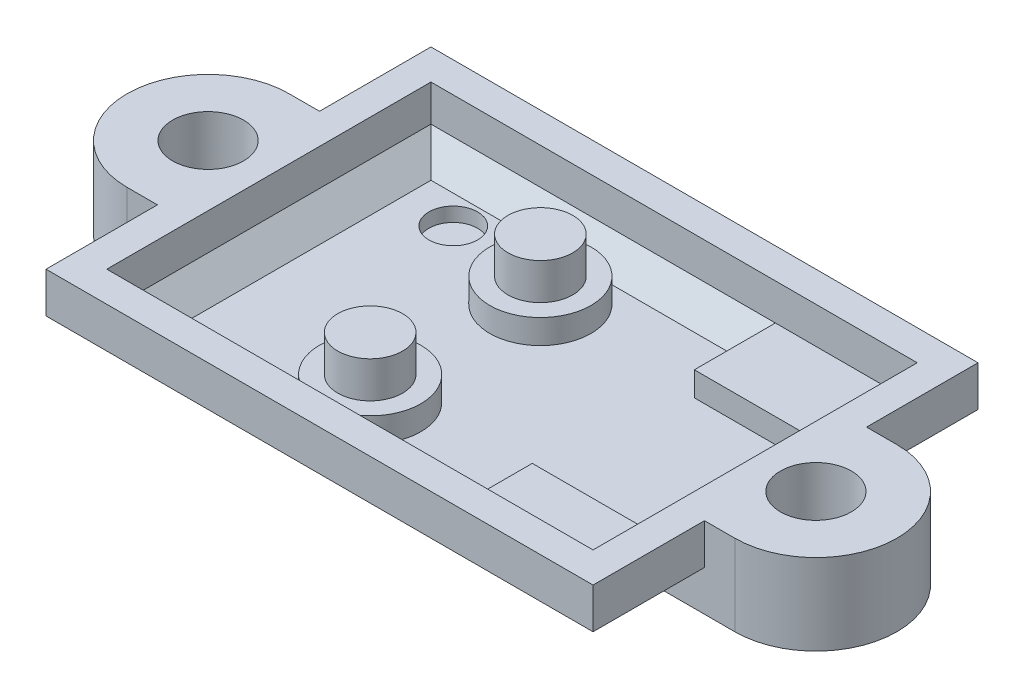
SolidWorks part; units mm, degrees
material "ABS"
ref_plane "Спереди" through (0, 0, 0) normal (0, 0, 1) x (1, 0, 0)
ref_plane "Сверху" through (0, 0, 0) normal (0, 1, 0) x (1, 0, 0)
ref_plane "Справа" through (0, 0, 0) normal (1, 0, 0) x (0, 0, -1)
sketch "Размеры платы" plane through (0, 0, 0) normal (0, 1, 0) x (1, 0, 0)
  line L1 (-10.9, -6.95) -> (10.9, -6.95) construction
  line L2 (-10.9, -6.95) -> (-10.9, 6.95) construction
  line L3 (-10.9, 6.95) -> (10.9, 6.95) construction
  line L4 (10.9, -6.95) -> (10.9, 6.95) construction
  line L5 (-10.9, -6.95) -> (10.9, 6.95) construction
  line L6 (-10.9, 6.95) -> (10.9, -6.95) construction
  point P0 (0, 0)
sketch "Внешние стенки" plane through (0, 0, 0) normal (0, 1, 0) x (1, 0, 0)
  line L0 (-15, 4) -> (-13.5, 4)
  line L1 (13.5, -9.5) -> (-13.5, -9.5)
  line L2 (13.5, -9.5) -> (13.5, 9.5) construction
  line L3 (13.5, 9.5) -> (-13.5, 9.5)
  line L4 (-13.5, -9.5) -> (-13.5, 9.5) construction
  line L5 (13.5, -9.5) -> (-13.5, 9.5) construction
  line L6 (13.5, 9.5) -> (-13.5, -9.5) construction
  line L7 (-15, -4) -> (-13.5, -4)
  line L8 (-13.5, 4) -> (-13.5, 9.5)
  line L9 (-13.5, -4) -> (-13.5, -9.5)
  line L10 (15, 4) -> (13.5, 4)
  line L11 (13.5, 4) -> (13.5, 9.5)
  line L12 (15, -4) -> (13.5, -4)
  line L13 (13.5, -4) -> (13.5, -9.5)
  arc A0 (-15, 4) -> (-15, -4) centre (-15, 0) ccw
  arc A1 (15, 4) -> (15, -4) centre (15, 0) cw
  circle A2 centre (-15, 0) radius 1.75
  circle A3 centre (15, 0) radius 1.75
  point P1 (0, 0)
extrude "Бобышка-Вытянуть1" add sketch "Внешние стенки" along normal blind 4
chamfer "Фаска1" distance 1.5 angle 45 2 edges at (-15, 0, 1.75) (15, 0, 1.75)
sketch "Внутренняя полость" plane through (0, 4, 0) normal (0, 1, 0) x (1, 0, 0)
  line L1 (-12, -8) -> (12, -8)
  line L2 (-12, -8) -> (-12, 8)
  line L3 (-12, 8) -> (12, 8)
  line L4 (12, -8) -> (12, 8)
  line L5 (-12, -8) -> (12, 8) construction
  line L6 (-12, 8) -> (12, -8) construction
  circle A0 centre (-2.8, 4.2) radius 1.6
  circle A1 centre (-2.8, -4.2) radius 1.6
  point P0 (0, 0)
extrude "Вырез-Вытянуть1" cut sketch "Внутренняя полость" against normal blind 3
sketch "Упоры платы" plane through (0, 1, 0) normal (0, 1, 0) x (1, 0, 0)
  line L1 (12, -8) -> (5, -8)
  line L2 (12, -8) -> (12, -4)
  line L3 (12, -4) -> (5, -4)
  line L4 (5, -8) -> (5, -4)
  line L5 (12, -8) -> (5, -4) construction
  line L6 (12, -4) -> (5, -8) construction
  line L7 (12, 8) -> (5, 8)
  line L8 (12, 8) -> (12, 4)
  line L9 (12, 4) -> (5, 4)
  line L10 (5, 8) -> (5, 4)
  line L11 (12, 8) -> (5, 4) construction
  line L12 (12, 4) -> (5, 8) construction
  circle A1 centre (-2.8, -4.2) radius 2.5
  circle A2 centre (-2.8, 4.2) radius 2.5
  point P8 (8.5, -6)
  point P14 (8.5, 6)
extrude "Бобышка-Вытянуть2" add sketch "Упоры платы" along normal blind 1.2
sketch "Индикация" plane through (0, 1, 0) normal (0, 1, 0) x (1, 0, 0)
  circle A0 centre (-8.3, 5.4) radius 1.2
extrude "Вырез-Вытянуть2" cut sketch "Индикация" against normal blind 0.7
chamfer "Фаска2" distance 1.2 angle 45 4 edges at (12, 1, 0) (-3.5, 1, -8) (-12, 1, 0) (-3.5, 1, 8)
chamfer "Фаска3" distance 2 angle 45 6 edges at (-13.5, 0, -6.75) (13.5, 0, -6.75) (0, 0, -9.5) (-13.5, 0, 6.75) (13.5, 0, 6.75) (0, 0, 9.5)
